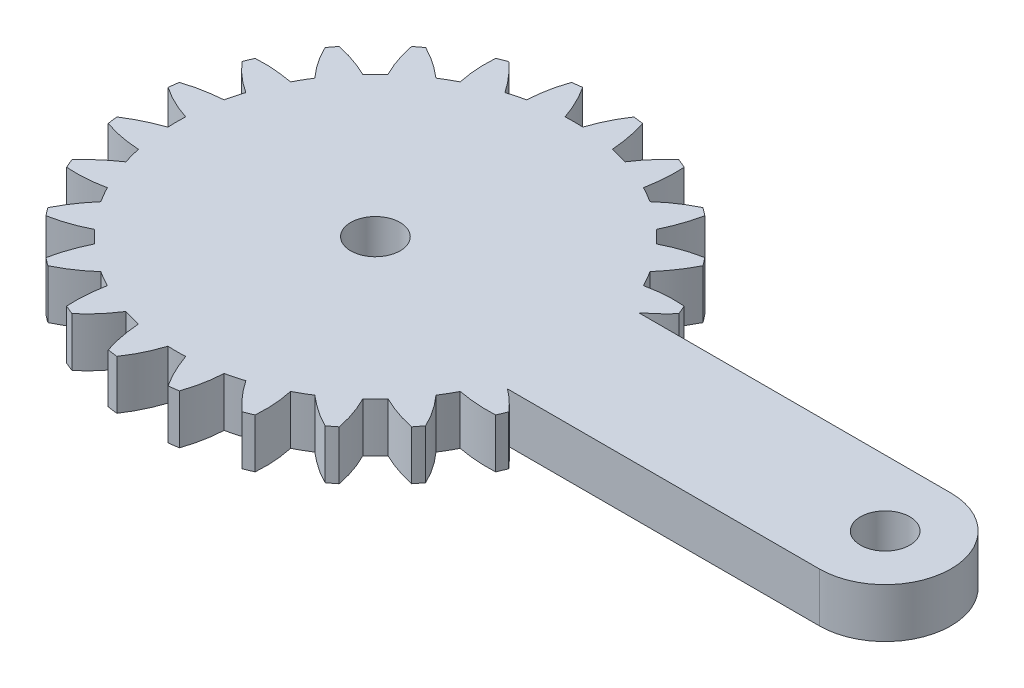
SolidWorks part; units mm, degrees
ref_plane "Front Plane" through (0, 0, 0) normal (0, 0, 1) x (1, 0, 0)
ref_plane "Top Plane" through (0, 0, 0) normal (0, 1, 0) x (1, 0, 0)
ref_plane "Right Plane" through (0, 0, 0) normal (1, 0, 0) x (0, 0, -1)
sketch "Sketch2" plane through (0, 0, 0) normal (0, 1, 0) x (1, 0, 0)
  line L0 (31, 4) -> (12.0129, 4)
  line L1 (31, -4) -> (12.0325, -4)
  line L2 (0, 0) -> (0, 12.09) construction
  line L3 (0, 0) -> (4.397, 16.4099) construction
  line L4 (0, 0) -> (-3.1291, 11.678) construction
  line L5 (-3.6882, 13.7644) -> (-4.4272, 16.5225) construction
  line L6 (0, 14.25) -> (0, 16.5009) construction
  line L7 (0, 0) -> (4.629, 11.1754) construction
  line L8 (4.629, 11.1754) -> (5.4532, 13.1653) construction
  circle A2 centre (31, 0) radius 1.5
  arc A3 (31, -4) -> (31, 4) centre (31, 0) ccw
  arc A12 (6.045, 10.4702) -> (5.5713, 10.7298) centre (0, 0) ccw
  arc A13 (3.6475, 11.5267) -> (3.1291, 11.678) centre (0, 0) ccw
  arc A81 (6.5065, 10.1899) -> (6.045, 10.4702) centre (0, 0) ccw
  arc A82 (8.5489, 8.5489) -> (8.1586, 8.9222) centre (0, 0) ccw
  circle A85 centre (0, 0) radius 1.5
  arc A87 (8.9148, 11.117) -> (8.4309, 11.4884) centre (0, 0) ccw
  arc A89 (8.9221, 8.1587) -> (8.5489, 8.5489) centre (0, 0) ccw
  arc A95 (10.4702, 6.045) -> (10.1898, 6.5066) centre (0, 0) ccw
  arc A97 (11.4884, 8.4309) -> (11.117, 8.9148) centre (0, 0) ccw
  arc A98 (10.7297, 5.5714) -> (10.4702, 6.045) centre (0, 0) ccw
  arc A100 (13.279, 5.1702) -> (13.0455, 5.7338) centre (0, 0) ccw
  arc A115 (10.4702, -6.045) -> (10.7298, -5.5713) centre (0, 0) ccw
  arc A117 (13.0455, -5.7338) -> (13.279, -5.1702) centre (0, 0) ccw
  arc A121 (5.7338, 13.0455) -> (5.1702, 13.279) centre (0, 0) ccw
  arc A161 (10.1899, -6.5065) -> (10.4702, -6.045) centre (0, 0) ccw
  arc A162 (8.5489, -8.5489) -> (8.9222, -8.1586) centre (0, 0) ccw
  arc A163 (11.117, -8.9148) -> (11.4884, -8.4309) centre (0, 0) ccw
  arc A164 (8.1587, -8.9221) -> (8.5489, -8.5489) centre (0, 0) ccw
  arc A165 (6.045, -10.4702) -> (6.5066, -10.1898) centre (0, 0) ccw
  arc A166 (8.4309, -11.4884) -> (8.9148, -11.117) centre (0, 0) ccw
  arc A167 (5.5714, -10.7297) -> (6.045, -10.4702) centre (0, 0) ccw
  arc A168 (3.1291, -11.678) -> (3.6476, -11.5266) centre (0, 0) ccw
  arc A169 (5.1702, -13.279) -> (5.7338, -13.0455) centre (0, 0) ccw
  arc A170 (2.6045, -11.8061) -> (3.1291, -11.678) centre (0, 0) ccw
  arc A171 (0, -12.09) -> (0.54, -12.0779) centre (0, 0) ccw
  arc A172 (1.5572, -14.1647) -> (2.162, -14.085) centre (0, 0) ccw
  arc A173 (-0.5399, -12.0779) -> (0, -12.09) centre (0, 0) ccw
  arc A174 (-3.1291, -11.678) -> (-2.6044, -11.8062) centre (0, 0) ccw
  arc A175 (-2.162, -14.085) -> (-1.5572, -14.1647) centre (0, 0) ccw
  arc A176 (-3.6475, -11.5267) -> (-3.1291, -11.678) centre (0, 0) ccw
  arc A177 (-6.045, -10.4702) -> (-5.5713, -10.7298) centre (0, 0) ccw
  arc A178 (-5.7338, -13.0455) -> (-5.1702, -13.279) centre (0, 0) ccw
  arc A179 (-6.5065, -10.1899) -> (-6.045, -10.4702) centre (0, 0) ccw
  arc A180 (-8.5489, -8.5489) -> (-8.1586, -8.9222) centre (0, 0) ccw
  arc A181 (-8.9148, -11.117) -> (-8.4309, -11.4884) centre (0, 0) ccw
  arc A182 (-8.9221, -8.1587) -> (-8.5489, -8.5489) centre (0, 0) ccw
  arc A183 (-10.4702, -6.045) -> (-10.1898, -6.5066) centre (0, 0) ccw
  arc A184 (-11.4884, -8.4309) -> (-11.117, -8.9148) centre (0, 0) ccw
  arc A185 (-10.7297, -5.5714) -> (-10.4702, -6.045) centre (0, 0) ccw
  arc A186 (-11.678, -3.1291) -> (-11.5266, -3.6476) centre (0, 0) ccw
  arc A187 (-13.279, -5.1702) -> (-13.0455, -5.7338) centre (0, 0) ccw
  arc A188 (-11.8061, -2.6045) -> (-11.678, -3.1291) centre (0, 0) ccw
  arc A189 (-12.09, 0) -> (-12.0779, -0.54) centre (0, 0) ccw
  arc A190 (-14.1647, -1.5572) -> (-14.085, -2.162) centre (0, 0) ccw
  arc A191 (-12.0779, 0.5399) -> (-12.09, 0) centre (0, 0) ccw
  arc A192 (-11.678, 3.1291) -> (-11.8062, 2.6044) centre (0, 0) ccw
  arc A193 (-14.085, 2.162) -> (-14.1647, 1.5572) centre (0, 0) ccw
  arc A194 (-11.5267, 3.6475) -> (-11.678, 3.1291) centre (0, 0) ccw
  arc A195 (-10.4702, 6.045) -> (-10.7298, 5.5713) centre (0, 0) ccw
  arc A196 (-13.0455, 5.7338) -> (-13.279, 5.1702) centre (0, 0) ccw
  arc A197 (-10.1899, 6.5065) -> (-10.4702, 6.045) centre (0, 0) ccw
  arc A198 (-8.5489, 8.5489) -> (-8.9222, 8.1586) centre (0, 0) ccw
  arc A199 (-11.117, 8.9148) -> (-11.4884, 8.4309) centre (0, 0) ccw
  arc A200 (-8.1587, 8.9221) -> (-8.5489, 8.5489) centre (0, 0) ccw
  arc A201 (-6.045, 10.4702) -> (-6.5066, 10.1898) centre (0, 0) ccw
  arc A202 (-8.4309, 11.4884) -> (-8.9148, 11.117) centre (0, 0) ccw
  arc A203 (-5.5714, 10.7297) -> (-6.045, 10.4702) centre (0, 0) ccw
  arc A204 (-3.1291, 11.678) -> (-3.6476, 11.5266) centre (0, 0) ccw
  arc A205 (-5.1702, 13.279) -> (-5.7338, 13.0455) centre (0, 0) ccw
  arc A206 (-2.6045, 11.8061) -> (-3.1291, 11.678) centre (0, 0) ccw
  arc A207 (0, 12.09) -> (-0.54, 12.0779) centre (0, 0) ccw
  arc A208 (-1.5572, 14.1647) -> (-2.162, 14.085) centre (0, 0) ccw
  arc A209 (0.5399, 12.0779) -> (0, 12.09) centre (0, 0) ccw
  arc A210 (3.1291, 11.678) -> (2.6044, 11.8062) centre (0, 0) ccw
  arc A211 (2.162, 14.085) -> (1.5572, 14.1647) centre (0, 0) ccw
  arc A212 (12.09, 0) -> (12.0779, 0.54) centre (0, 0) ccw [skipped]
  arc A213 (14.1647, 1.5572) -> (14.085, 2.162) centre (0, 0) ccw [skipped]
  arc A214 (12.0779, -0.5399) -> (12.09, 0) centre (0, 0) ccw [skipped]
  arc A215 (11.678, -3.1291) -> (11.8062, -2.6044) centre (0, 0) ccw [skipped]
  arc A216 (14.085, -2.162) -> (14.1647, -1.5572) centre (0, 0) ccw [skipped]
  arc A217 (11.5267, -3.6475) -> (11.678, -3.1291) centre (0, 0) ccw [skipped]
  arc A218 (11.8061, 2.6045) -> (11.678, 3.1291) centre (0, 0) ccw [skipped]
  arc A219 (11.678, 3.1291) -> (11.5266, 3.6476) centre (0, 0) ccw [skipped]
  spline S0 degree 3 poles (8.9148, 11.117) (8.7604, 10.3435) (8.4826, 9.6001) (8.1586, 8.9222) knots 0.154713 0.154713 0.154713 0.154713 1 1 1 1
  spline S1 degree 3 poles (6.5065, 10.1899) (7.0658, 10.6979) (7.7126, 11.1471) (8.4309, 11.4884) knots 0 0 0 0 0.845227 0.845227 0.845227 0.845227
  spline S2 degree 3 poles (11.4884, 8.4309) (11.139, 7.7237) (10.6783, 7.0775) (10.1898, 6.5066) knots 0.154713 0.154713 0.154713 0.154713 1 1 1 1
  spline S3 degree 3 poles (8.9221, 8.1587) (9.5939, 8.5047) (10.3348, 8.7711) (11.117, 8.9148) knots 0 0 0 0 0.845227 0.845227 0.845227 0.845227
  spline S4 degree 3 poles (3.6475, 11.5267) (4.0562, 12.1622) (4.5647, 12.7634) (5.1702, 13.279) knots 0 0 0 0 0.845227 0.845227 0.845227 0.845227
  spline S5 degree 3 poles (5.7338, 13.0455) (5.7848, 12.2584) (5.7089, 11.4685) (5.5713, 10.7298) knots 0.154713 0.154713 0.154713 0.154713 1 1 1 1
  spline S6 degree 3 poles (13.279, 5.1702) (12.8955, 4.7335) (12.4622, 4.3445) (12.0129, 4) knots 0.154713 0.154713 0.154713 0.154713 0.77749 0.77749 0.77749 0.77749
  spline S7 degree 3 poles (10.7297, 5.5714) (11.4681, 5.7318) (12.2528, 5.7974) (13.0455, 5.7338) knots 0 0 0 0 0.845227 0.845227 0.845227 0.845227
  spline S12 degree 3 poles (13.0455, -5.7338) (12.2584, -5.7848) (11.4685, -5.7089) (10.7298, -5.5713) knots 0.154713 0.154713 0.154713 0.154713 1 1 1 1
  spline S13 degree 3 poles (12.0325, -4) (12.4803, -4.3376) (12.9025, -4.728) (13.279, -5.1702) knots 0.228019 0.228019 0.228019 0.228019 0.845227 0.845227 0.845227 0.845227
  spline S14 degree 3 poles (11.117, -8.9148) (10.3435, -8.7604) (9.6001, -8.4826) (8.9222, -8.1586) knots 0.154713 0.154713 0.154713 0.154713 1 1 1 1
  spline S15 degree 3 poles (10.1899, -6.5065) (10.6979, -7.0658) (11.1471, -7.7126) (11.4884, -8.4309) knots 0 0 0 0 0.845227 0.845227 0.845227 0.845227
  spline S16 degree 3 poles (8.4309, -11.4884) (7.7237, -11.139) (7.0775, -10.6783) (6.5066, -10.1898) knots 0.154713 0.154713 0.154713 0.154713 1 1 1 1
  spline S17 degree 3 poles (8.1587, -8.9221) (8.5047, -9.5939) (8.7711, -10.3348) (8.9148, -11.117) knots 0 0 0 0 0.845227 0.845227 0.845227 0.845227
  spline S18 degree 3 poles (5.1702, -13.279) (4.5775, -12.7584) (4.0726, -12.1462) (3.6476, -11.5266) knots 0.154713 0.154713 0.154713 0.154713 1 1 1 1
  spline S19 degree 3 poles (5.5714, -10.7297) (5.7318, -11.4681) (5.7974, -12.2528) (5.7338, -13.0455) knots 0 0 0 0 0.845227 0.845227 0.845227 0.845227
  spline S20 degree 3 poles (1.5572, -14.1647) (1.1194, -13.5085) (0.7902, -12.7864) (0.54, -12.0779) knots 0.154713 0.154713 0.154713 0.154713 1 1 1 1
  spline S21 degree 3 poles (2.6045, -11.8061) (2.5683, -12.5609) (2.4286, -13.3358) (2.162, -14.085) knots 0 0 0 0 0.845227 0.845227 0.845227 0.845227
  spline S22 degree 3 poles (-2.162, -14.085) (-2.415, -13.3379) (-2.5461, -12.5553) (-2.6044, -11.8062) knots 0.154713 0.154713 0.154713 0.154713 1 1 1 1
  spline S23 degree 3 poles (-0.5399, -12.0779) (-0.7702, -12.7976) (-1.1057, -13.5099) (-1.5572, -14.1647) knots 0 0 0 0 0.845227 0.845227 0.845227 0.845227
  spline S24 degree 3 poles (-5.7338, -13.0455) (-5.7848, -12.2584) (-5.7089, -11.4685) (-5.5713, -10.7298) knots 0.154713 0.154713 0.154713 0.154713 1 1 1 1
  spline S25 degree 3 poles (-3.6475, -11.5267) (-4.0562, -12.1622) (-4.5647, -12.7634) (-5.1702, -13.279) knots 0 0 0 0 0.845227 0.845227 0.845227 0.845227
  spline S26 degree 3 poles (-8.9148, -11.117) (-8.7604, -10.3435) (-8.4826, -9.6001) (-8.1586, -8.9222) knots 0.154713 0.154713 0.154713 0.154713 1 1 1 1
  spline S27 degree 3 poles (-6.5065, -10.1899) (-7.0658, -10.6979) (-7.7126, -11.1471) (-8.4309, -11.4884) knots 0 0 0 0 0.845227 0.845227 0.845227 0.845227
  spline S28 degree 3 poles (-11.4884, -8.4309) (-11.139, -7.7237) (-10.6783, -7.0775) (-10.1898, -6.5066) knots 0.154713 0.154713 0.154713 0.154713 1 1 1 1
  spline S29 degree 3 poles (-8.9221, -8.1587) (-9.5939, -8.5047) (-10.3348, -8.7711) (-11.117, -8.9148) knots 0 0 0 0 0.845227 0.845227 0.845227 0.845227
  spline S30 degree 3 poles (-13.279, -5.1702) (-12.7584, -4.5775) (-12.1462, -4.0726) (-11.5266, -3.6476) knots 0.154713 0.154713 0.154713 0.154713 1 1 1 1
  spline S31 degree 3 poles (-10.7297, -5.5714) (-11.4681, -5.7318) (-12.2528, -5.7974) (-13.0455, -5.7338) knots 0 0 0 0 0.845227 0.845227 0.845227 0.845227
  spline S32 degree 3 poles (-14.1647, -1.5572) (-13.5085, -1.1194) (-12.7864, -0.7902) (-12.0779, -0.54) knots 0.154713 0.154713 0.154713 0.154713 1 1 1 1
  spline S33 degree 3 poles (-11.8061, -2.6045) (-12.5609, -2.5683) (-13.3358, -2.4286) (-14.085, -2.162) knots 0 0 0 0 0.845227 0.845227 0.845227 0.845227
  spline S34 degree 3 poles (-14.085, 2.162) (-13.3379, 2.415) (-12.5553, 2.5461) (-11.8062, 2.6044) knots 0.154713 0.154713 0.154713 0.154713 1 1 1 1
  spline S35 degree 3 poles (-12.0779, 0.5399) (-12.7976, 0.7702) (-13.5099, 1.1057) (-14.1647, 1.5572) knots 0 0 0 0 0.845227 0.845227 0.845227 0.845227
  spline S36 degree 3 poles (-13.0455, 5.7338) (-12.2584, 5.7848) (-11.4685, 5.7089) (-10.7298, 5.5713) knots 0.154713 0.154713 0.154713 0.154713 1 1 1 1
  spline S37 degree 3 poles (-11.5267, 3.6475) (-12.1622, 4.0562) (-12.7634, 4.5647) (-13.279, 5.1702) knots 0 0 0 0 0.845227 0.845227 0.845227 0.845227
  spline S38 degree 3 poles (-11.117, 8.9148) (-10.3435, 8.7604) (-9.6001, 8.4826) (-8.9222, 8.1586) knots 0.154713 0.154713 0.154713 0.154713 1 1 1 1
  spline S39 degree 3 poles (-10.1899, 6.5065) (-10.6979, 7.0658) (-11.1471, 7.7126) (-11.4884, 8.4309) knots 0 0 0 0 0.845227 0.845227 0.845227 0.845227
  spline S40 degree 3 poles (-8.4309, 11.4884) (-7.7237, 11.139) (-7.0775, 10.6783) (-6.5066, 10.1898) knots 0.154713 0.154713 0.154713 0.154713 1 1 1 1
  spline S41 degree 3 poles (-8.1587, 8.9221) (-8.5047, 9.5939) (-8.7711, 10.3348) (-8.9148, 11.117) knots 0 0 0 0 0.845227 0.845227 0.845227 0.845227
  spline S42 degree 3 poles (-5.1702, 13.279) (-4.5775, 12.7584) (-4.0726, 12.1462) (-3.6476, 11.5266) knots 0.154713 0.154713 0.154713 0.154713 1 1 1 1
  spline S43 degree 3 poles (-5.5714, 10.7297) (-5.7318, 11.4681) (-5.7974, 12.2528) (-5.7338, 13.0455) knots 0 0 0 0 0.845227 0.845227 0.845227 0.845227
  spline S44 degree 3 poles (-1.5572, 14.1647) (-1.1194, 13.5085) (-0.7902, 12.7864) (-0.54, 12.0779) knots 0.154713 0.154713 0.154713 0.154713 1 1 1 1
  spline S45 degree 3 poles (-2.6045, 11.8061) (-2.5683, 12.5609) (-2.4286, 13.3358) (-2.162, 14.085) knots 0 0 0 0 0.845227 0.845227 0.845227 0.845227
  spline S46 degree 3 poles (2.162, 14.085) (2.415, 13.3379) (2.5461, 12.5553) (2.6044, 11.8062) knots 0.154713 0.154713 0.154713 0.154713 1 1 1 1
  spline S47 degree 3 poles (0.5399, 12.0779) (0.7702, 12.7976) (1.1057, 13.5099) (1.5572, 14.1647) knots 0 0 0 0 0.845227 0.845227 0.845227 0.845227
  point P11 (0, 12.09)
  point P15 (-3.1291, 11.678)
  point P167 (0, 0)
  point P177 (0, 0)
  dimension "D1" = 3
  dimension "D2" = 8
  dimension "D7" = 24
  dimension "D8" = 3.1561
  dimension "D6" = 24
  dimension "D15" = 0.61
  dimension "D3" = 31
  dimension "D4" = 15
  dimension "D5" = 15
  dimension "D16" = 7.5
  dimension "D17" = 180
extrude "Boss-Extrude1" add sketch "Sketch2" along normal blind 3
